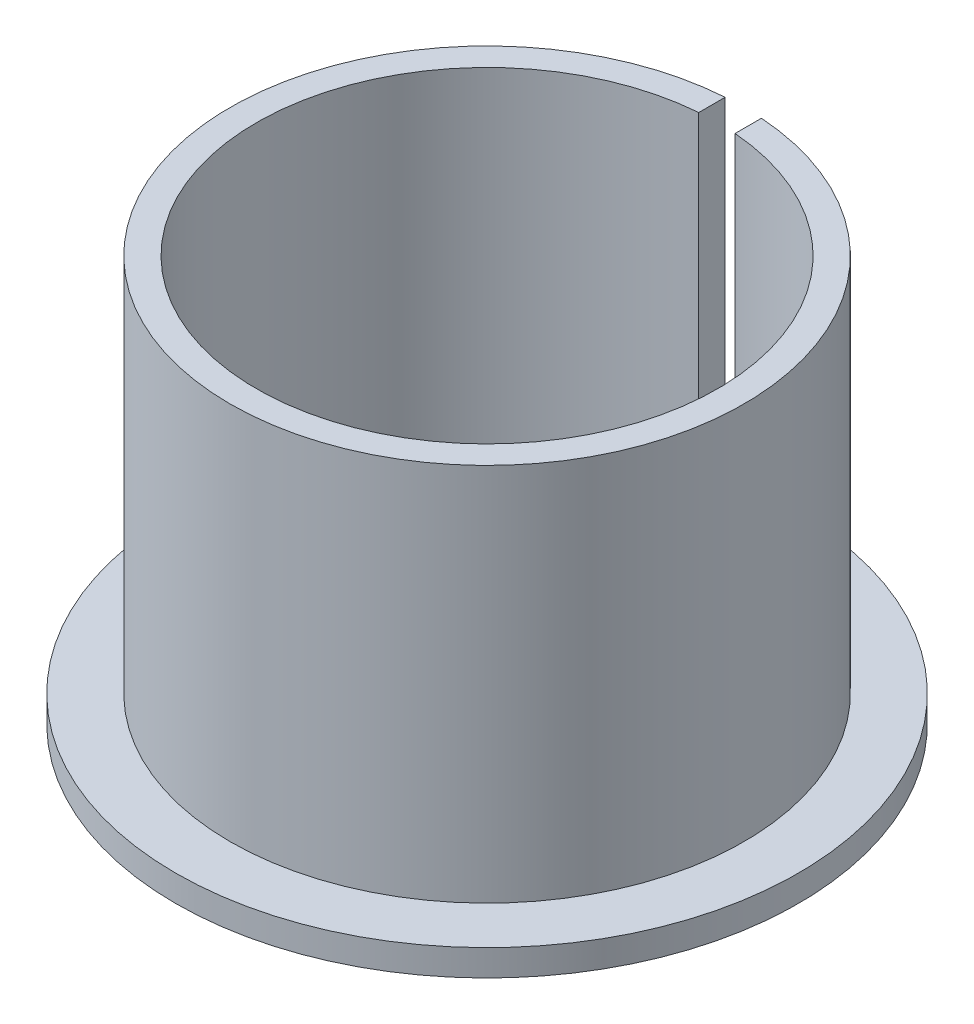
SolidWorks part; units mm, degrees
ref_plane "Front" through (0, 0, 0) normal (0, 0, 1) x (1, 0, 0)
ref_plane "Top" through (0, 0, 0) normal (0, 1, 0) x (1, 0, 0)
ref_plane "Right" through (0, 0, 0) normal (1, 0, 0) x (0, 0, -1)
sketch "Sketch1" plane through (0, 0, 0) normal (0, 0, 1) x (1, 0, 0)
  line L0 (12.7, 2.7894) -> (12.7, 25.1194)
  line L1 (12.7, 25.1194) -> (14.15, 25.1194)
  line L2 (14.15, 25.1194) -> (14.15, 4.2394)
  line L3 (14.15, 4.2394) -> (17.15, 4.2394)
  line L4 (17.15, 4.2394) -> (17.15, 2.7894)
  line L5 (17.15, 2.7894) -> (12.7, 2.7894)
  line L6 (0, 0) -> (0, 40.101) construction
  dimension "D1" = 20.88
  dimension "D2" = 14.15
  dimension "D3" = 12.7
  dimension "D4" = 3
revolve "Revolve1" add sketch "Sketch1" angle 360 about L6
sketch "Sketch2" plane through (0, 25.1194, 0) normal (0, 1, 0) x (1, 0, 0)
  line L0 (-1, 60.0408) -> (-1, -6.0526)
  line L1 (-1, 60.0408) -> (1, 60.0408)
  line L2 (-1, -6.0526) -> (1, -6.0526)
  line L3 (1, 60.0408) -> (1, -6.0526)
  line L4 (0, -6.0526) -> (0, 0)
  dimension "D1" = 2
extrude "Cut-Extrude1" cut sketch "Sketch2" against normal through all contours L0 L2 L3 L1
